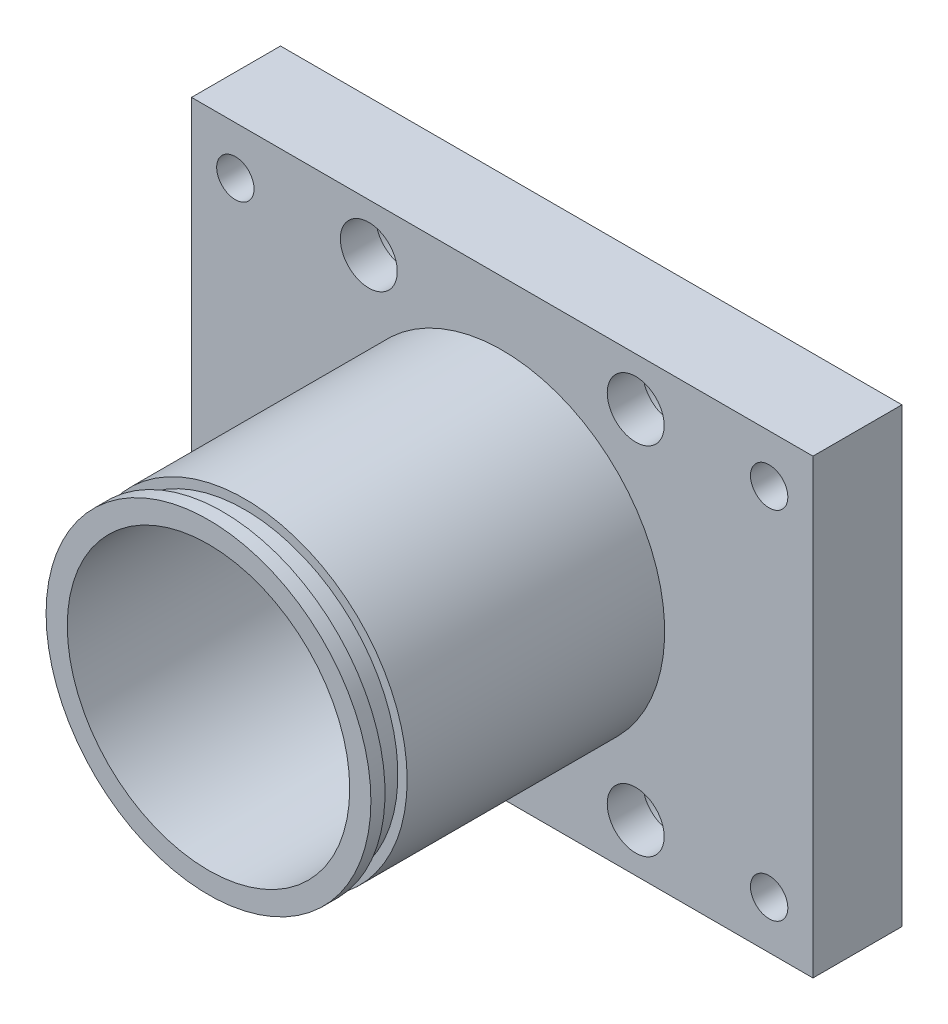
SolidWorks part; units mm, degrees
ref_plane "Front Plane" through (0, 0, 0) normal (0, 0, 1) x (1, 0, 0)
ref_plane "Top Plane" through (0, 0, 0) normal (0, 1, 0) x (1, 0, 0)
ref_plane "Right Plane" through (0, 0, 0) normal (1, 0, 0) x (0, 0, -1)
sketch "Sketch1" plane through (0, 0, 0) normal (0, 0, 1) x (1, 0, 0)
  line L1 (-34.925, -25.4) -> (34.925, -25.4)
  line L2 (-34.925, -25.4) -> (-34.925, 25.4)
  line L3 (-34.925, 25.4) -> (34.925, 25.4)
  line L4 (34.925, -25.4) -> (34.925, 25.4)
  line L5 (-34.925, -25.4) -> (34.925, 25.4) construction
  line L6 (-34.925, 25.4) -> (34.925, -25.4) construction
  point P0 (0, 0)
  dimension "D1" = 50.8
  dimension "D2" = 69.85
extrude "Boss-Extrude1" add sketch "Sketch1" along normal blind 10
sketch "Sketch2" plane through (0, 0, 10) normal (0, 0, 1) x (1, 0, 0)
  circle A0 centre (0, 0) radius 15.875
  dimension "D1" = 31.75
extrude "Cut-Extrude1" cut sketch "Sketch2" against normal through all
hole_wizard "M5x0.8 Tapped Hole1" positions "Sketch4" profile "Sketch3" tap size "M5x0.8" standard "Ansi Metric" end condition through all
sketch "Sketch4" plane through (0, 0, 10) normal (0, 0, 1) x (1, 0, 0)
  line L0 (0, 26.8838) -> (0, -28.9382) construction
  line L3 (41.3352, 0) -> (-38.9975, 0) construction
  point P0 (30, 20)
  dimension "D1" = 30
  dimension "D2" = 20
sketch "Sketch3" plane through (30, 20, 10) normal (1, 0, 0) x (0, -1, 0)
  line L0 (0, 0) -> (0, 10)
  line L1 (0, 10) -> (2.1, 10)
  line L2 (2.1, 10) -> (2.1, 0)
  line L5 (2.1, 0) -> (0, 0)
  line L11 (0, -6.35) -> (0, 107.95) construction
  dimension "Thread Major Dia." = 4.2
  dimension "Thru Tap Drill Depth" = 10
hole_wizard "CBORE for M6 SHCS1" positions "Sketch6" profile "Sketch5" counterbore size "M6" standard "Ansi Metric" end condition through all
sketch "Sketch6" plane through (0, 0, 0) normal (0, 0, -1) x (-1, 0, 0)
  line L0 (0, 27.7339) -> (0, -28.6549) construction
  line L3 (39.6351, 0) -> (-38.8558, 0) construction
  point P0 (-15, 20)
  dimension "D1" = 15
  dimension "D2" = 20
sketch "Sketch5" plane through (15, 20, 0) normal (1, 0, 0) x (0, 1, 0)
  line L0 (0, 0) -> (0, 10)
  line L1 (0, 10) -> (3.2, 10)
  line L3 (3.2, 10) -> (3.2, 6)
  line L4 (3.2, 6) -> (5.05, 6)
  line L5 (5.05, 6) -> (5.05, 0)
  line L7 (5.05, 0) -> (0, 0)
  line L11 (0, -6.35) -> (0, 107.95) construction
  dimension "Thru Hole Dia." = 6.4
  dimension "Thru Hole Depth" = 10
  dimension "C'Bore Dia." = 10.1
  dimension "C'Bore Depth" = 6
mirror "Mirror1" about plane through (0, 0, 0) normal (0, 1, 0) of "CBORE for M6 SHCS1", "M5x0.8 Tapped Hole1"
mirror "Mirror2" about plane through (0, 0, 0) normal (1, 0, 0) of "Mirror1", "M5x0.8 Tapped Hole1", "CBORE for M6 SHCS1"
sketch "Sketch7" plane through (0, 0, 10) normal (0, 0, 1) x (1, 0, 0)
  circle A0 centre (0, 0) radius 15.875
  circle A1 centre (0, 0) radius 18.2562
  dimension "D1" = 36.5125
extrude "Boss-Extrude2" add sketch "Sketch7" along normal blind 33.02
sketch "Sketch8" plane through (0, 0, 0) normal (0, 0, -1) x (-1, 0, 0)
  circle A0 centre (0, 0) radius 16.6687
  circle A1 centre (0, 0) radius 18.8531
  dimension "D1" = 33.3375
  dimension "D2" = 2.1844
extrude "Cut-Extrude2" cut sketch "Sketch8" against normal blind 1.3208
sketch "Sketch9" plane through (0, 0, 0) normal (1, 0, 0) x (0, 0, -1)
  line L0 (-43.02, -18.6844) -> (-43.02, -15.4639) construction
  line L1 (-38.9433, -17.211) -> (-41.4325, -17.211)
  line L2 (-38.9433, -17.211) -> (-38.9433, -18.5064)
  line L3 (-38.9433, -18.5064) -> (-41.4325, -18.5064)
  line L4 (-41.4325, -17.211) -> (-41.4325, -18.5064)
  line L5 (-38.9433, -17.211) -> (-41.4325, -18.5064) construction
  line L6 (-38.9433, -18.5064) -> (-41.4325, -17.211) construction
  line L7 (-43.02, 18.2562) -> (-43.02, -18.2562) construction
  line L8 (4.3912, 0) -> (-56.8555, 0) construction
  point P0 (-40.1879, -17.8587)
  dimension "D1" = 2.4892
  dimension "D2" = 17.211
  dimension "D3" = 3.175
  dimension "D4" = 1.2954
revolve "Cut-Revolve1" cut sketch "Sketch9" angle 360 about L8
